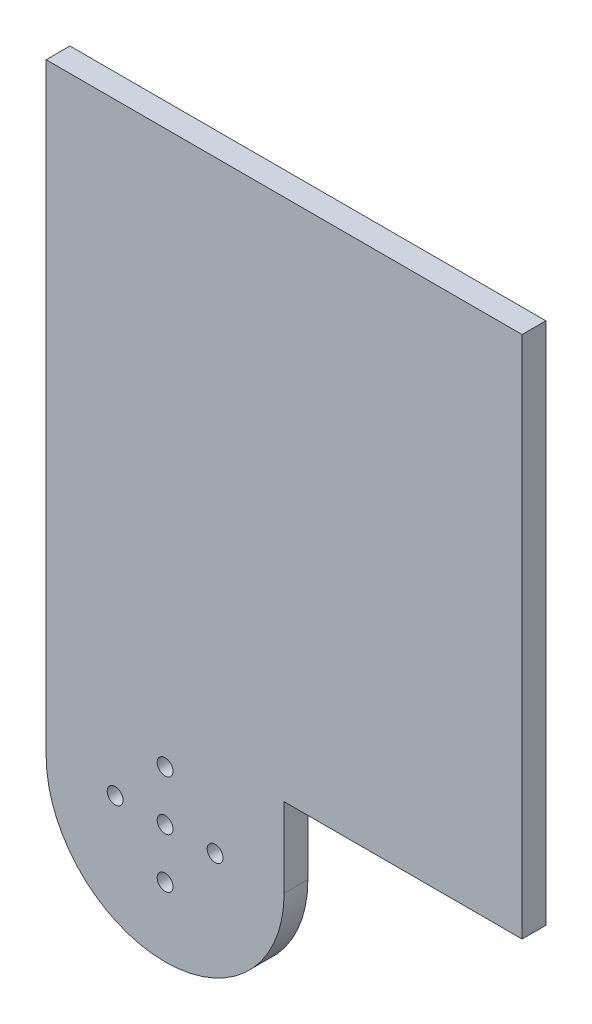
SolidWorks part; units mm, degrees
ref_plane "前基準面" through (0, 0, 0) normal (0, 0, 1) x (1, 0, 0)
ref_plane "上基準面" through (0, 0, 0) normal (0, 1, 0) x (1, 0, 0)
ref_plane "右基準面" through (0, 0, 0) normal (1, 0, 0) x (0, 0, -1)
sketch "草圖1" plane through (0, 0, 0) normal (0, 0, 1) x (1, 0, 0)
  line L0 (-15, 0) -> (-15, 76)
  line L1 (-15, 76) -> (15, 76)
  line L2 (15, 76) -> (15, 0)
  circle A0 centre (0, 0) radius 15
  circle A1 centre (0, 0) radius 1
  circle A2 centre (6.3, 0) radius 1
  circle A3 centre (0, -6.3) radius 1
  circle A4 centre (-6.3, 0) radius 1
  circle A5 centre (0, 6.3) radius 1
  point P15 (0, 0)
  dimension "D1" = 30
  dimension "D2" = 2
  dimension "D3" = 2
  dimension "D4" = 6.3
  dimension "D6" = 6.3
  dimension "D7" = 76
  dimension "D5" = 4
extrude "填料-伸長1" add sketch "草圖1" against normal blind 3 contours A0 A5 A4 A3 A2 A1 | A0 L2 L1 L0
sketch "草圖2" plane through (15, 0, 0) normal (1, 0, 0) x (0, 0, -1)
  line L0 (0, 76) -> (3, 76)
  line L1 (3, 76) -> (3, 10)
  line L3 (0, 10) -> (0, 76)
  line L4 (0, 10) -> (3, 10)
  dimension "D1" = 66
extrude "填料-伸長2" add sketch "草圖2" along normal blind 30
